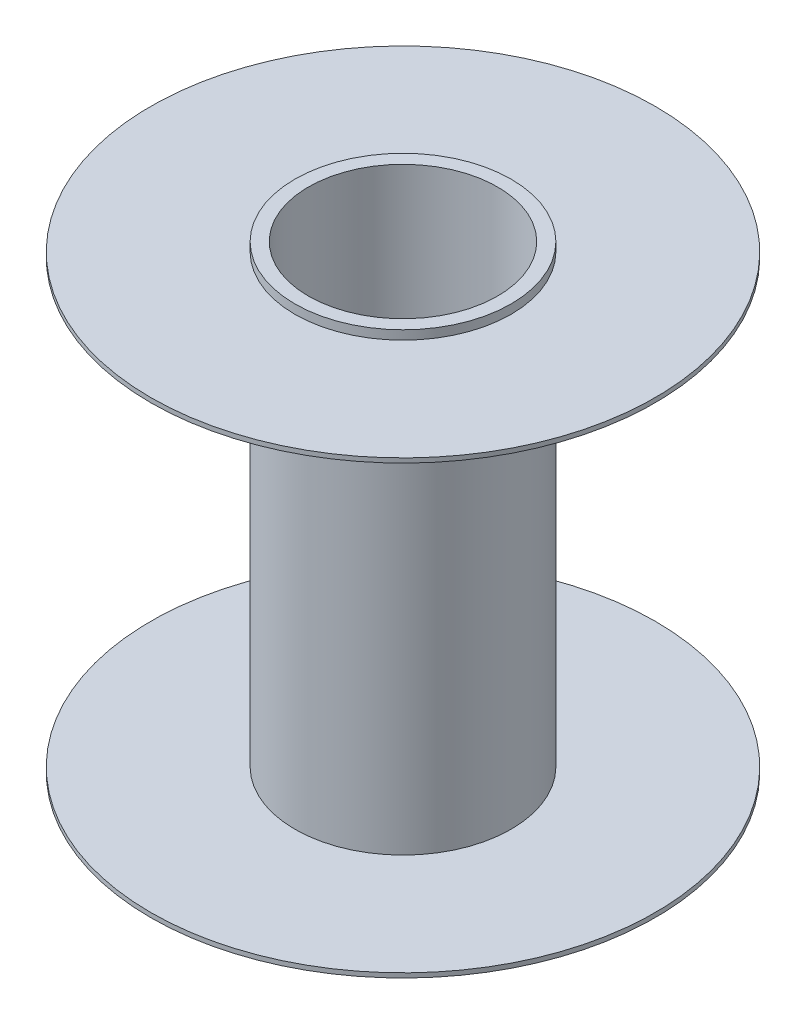
SolidWorks part; units mm, degrees
ref_plane "Alzado" through (0, 0, 0) normal (0, 0, 1) x (1, 0, 0)
ref_plane "Planta" through (0, 0, 0) normal (0, 1, 0) x (1, 0, 0)
ref_plane "Vista lateral" through (0, 0, 0) normal (1, 0, 0) x (0, 0, -1)
sketch "Croquis1" plane through (0, 0, 0) normal (0, 1, 0) x (1, 0, 0)
  circle A0 centre (0, 0) radius 2.1
  circle A1 centre (0, 0) radius 2.4
extrude "Saliente-Extruir1" add sketch "Croquis1" along normal blind 0.2
sketch "Croquis3" plane through (0, 0, 0) normal (0, -1, 0) x (1, 0, 0)
  circle A0 centre (0, 0) radius 5.6
  circle A1 centre (0, 0) radius 2.3
extrude "Saliente-Extruir2" add sketch "Croquis3" along normal blind 0.1 separate body
sketch "Croquis5" plane through (0, 0, 0) normal (0, -1, 0) x (1, 0, 0)
  circle A0 centre (0, 0) radius 2.1 construction
  circle A1 centre (0, 0) radius 2.4
  circle A2 centre (0, 0) radius 2.4
  circle A3 centre (0, 0) radius 2.1
  dimension "D1" = 0
extrude "Saliente-Extruir3" add sketch "Croquis5" along normal blind 5
ref_plane "Plano1" through (0, -5, 0) normal (0, -1, 0) x (-1, 0, 0)
mirror "Simetría2" about plane through (0, -5, 0) normal (0, -1, 0) of "Saliente-Extruir2", "Saliente-Extruir3", "Saliente-Extruir1"
